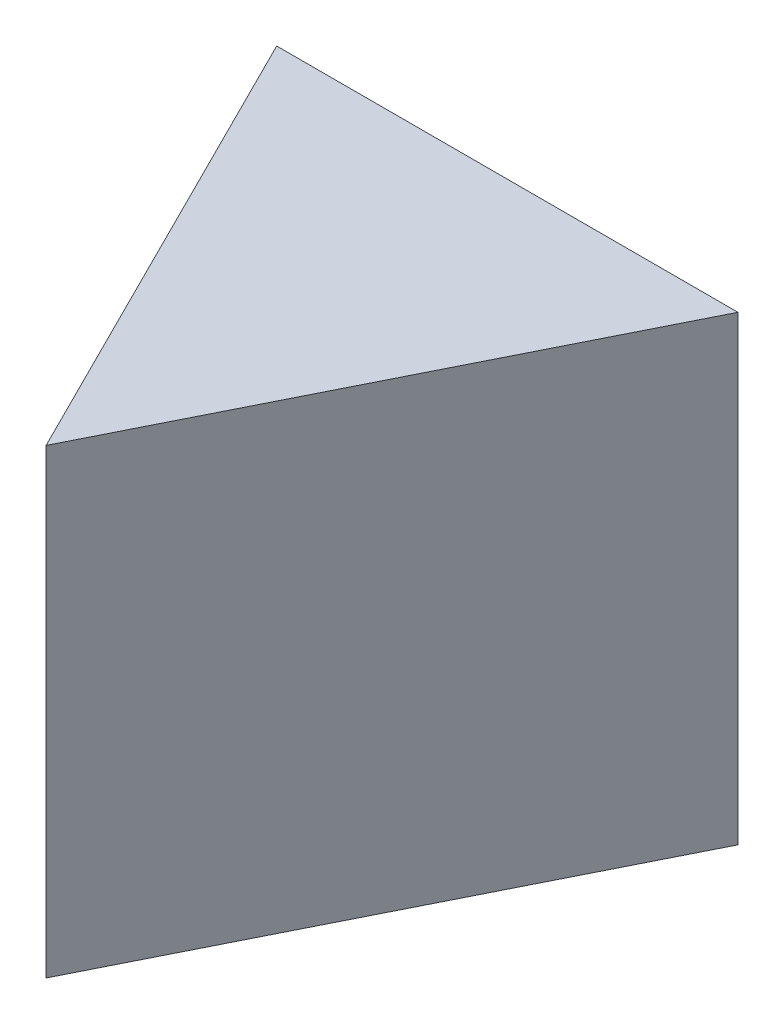
SolidWorks part; units mm, degrees
ref_plane "Front Plane" through (0, 0, 0) normal (0, 0, 1) x (1, 0, 0)
ref_plane "Top Plane" through (0, 0, 0) normal (0, 1, 0) x (1, 0, 0)
ref_plane "Right Plane" through (0, 0, 0) normal (1, 0, 0) x (0, 0, -1)
sketch "Sketch1" plane through (0, 0, 0) normal (0, 0, 1) x (1, 0, 0)
  line L1 (0, 0) -> (20, 0)
  line L2 (0, 0) -> (0, 20)
  line L3 (0, 20) -> (20, 20)
  line L4 (20, 0) -> (20, 20)
  dimension "D1" = 20
  dimension "D2" = 20
extrude "Boss-Extrude1" add sketch "Sketch1" along normal blind 20
sketch "Sketch2" plane through (0, 20, 0) normal (0, 1, 0) x (1, 0, 0)
  line L0 (0, 0) -> (10, -20)
  line L1 (20, -20) -> (0, -20) construction
  line L2 (10, -20) -> (0, -20)
  line L3 (0, -20) -> (0, 0)
extrude "Cut-Extrude1" cut sketch "Sketch2" against normal blind 20
sketch "Sketch3" plane through (0, 20, 0) normal (0, 1, 0) x (1, 0, 0)
  line L0 (20, 0) -> (10, -20)
  line L1 (10, -20) -> (20, -20)
  line L2 (20, -20) -> (20, 0)
extrude "Cut-Extrude2" cut sketch "Sketch3" against normal blind 20
